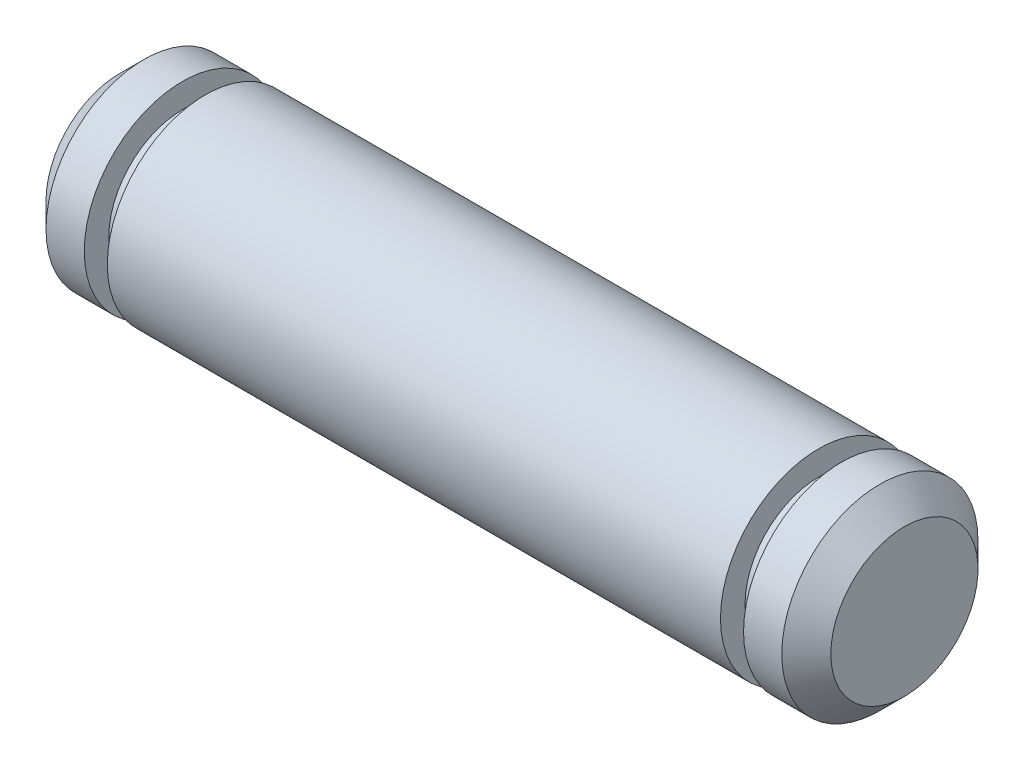
SolidWorks part; units mm, degrees
ref_plane "Front Plane" through (0, 0, 0) normal (0, 0, 1) x (1, 0, 0)
ref_plane "Top Plane" through (0, 0, 0) normal (0, 1, 0) x (1, 0, 0)
ref_plane "Right Plane" through (0, 0, 0) normal (1, 0, 0) x (0, 0, -1)
ref_plane "Plane1" through (0, 0, 0) normal (0, 0, 1) x (1, 0, 0)
sketch "Sketch1" plane through (0, 0, 0) normal (0, 0, 1) x (1, 0, 0)
  line L0 (-16, 0) -> (-16, 4)
  line L1 (-16, 4) -> (16, 4)
  line L2 (16, 4) -> (16, 0)
  line L3 (16, 0) -> (-16, 0)
  line L4 (16, 0) -> (-16, 0) construction
revolve "Revolve1" add sketch "Sketch1" angle 360 about L4
ref_plane "Plane2" through (0, 0, 0) normal (0, 0, 1) x (1, 0, 0)
sketch "Sketch2" plane through (0, 0, 0) normal (0, 0, 1) x (1, 0, 0)
  line L0 (15, 4) -> (16, 3)
  line L1 (16, 3) -> (16, 4)
  line L2 (16, 4) -> (15, 4)
  line L3 (16, 0) -> (-16, 0) construction
revolve "Cut-Revolve1" cut sketch "Sketch2" angle 360 about L3
ref_plane "Plane3" through (0, 0, 0) normal (0, 0, 1) x (1, 0, 0)
sketch "Sketch3" plane through (0, 0, 0) normal (0, 0, 1) x (1, 0, 0)
  line L0 (-16, 3) -> (-15, 4)
  line L1 (-15, 4) -> (-16, 4)
  line L2 (-16, 4) -> (-16, 3)
  line L3 (16, 0) -> (-16, 0) construction
revolve "Cut-Revolve2" cut sketch "Sketch3" angle 360 about L3
ref_plane "Plane4" through (0, 0, 0) normal (0, 0, 1) x (1, 0, 0)
sketch "Sketch4" plane through (0, 0, 0) normal (0, 0, 1) x (1, 0, 0)
  line L0 (12.5, 3) -> (13.44, 3)
  line L1 (13.44, 3) -> (13.44, 4)
  line L2 (13.44, 4) -> (12.5, 4)
  line L3 (12.5, 4) -> (12.5, 3)
  line L4 (16, 0) -> (-16, 0) construction
revolve "Cut-Revolve3" cut sketch "Sketch4" angle 360 about L4
ref_plane "Plane5" through (0, 0, 0) normal (0, 0, 1) x (1, 0, 0)
sketch "Sketch5" plane through (0, 0, 0) normal (0, 0, 1) x (1, 0, 0)
  line L0 (-13.44, 3) -> (-12.5, 3)
  line L1 (-12.5, 3) -> (-12.5, 4)
  line L2 (-12.5, 4) -> (-13.44, 4)
  line L3 (-13.44, 4) -> (-13.44, 3)
  line L4 (16, 0) -> (-16, 0) construction
revolve "Cut-Revolve4" cut sketch "Sketch5" angle 360 about L4
